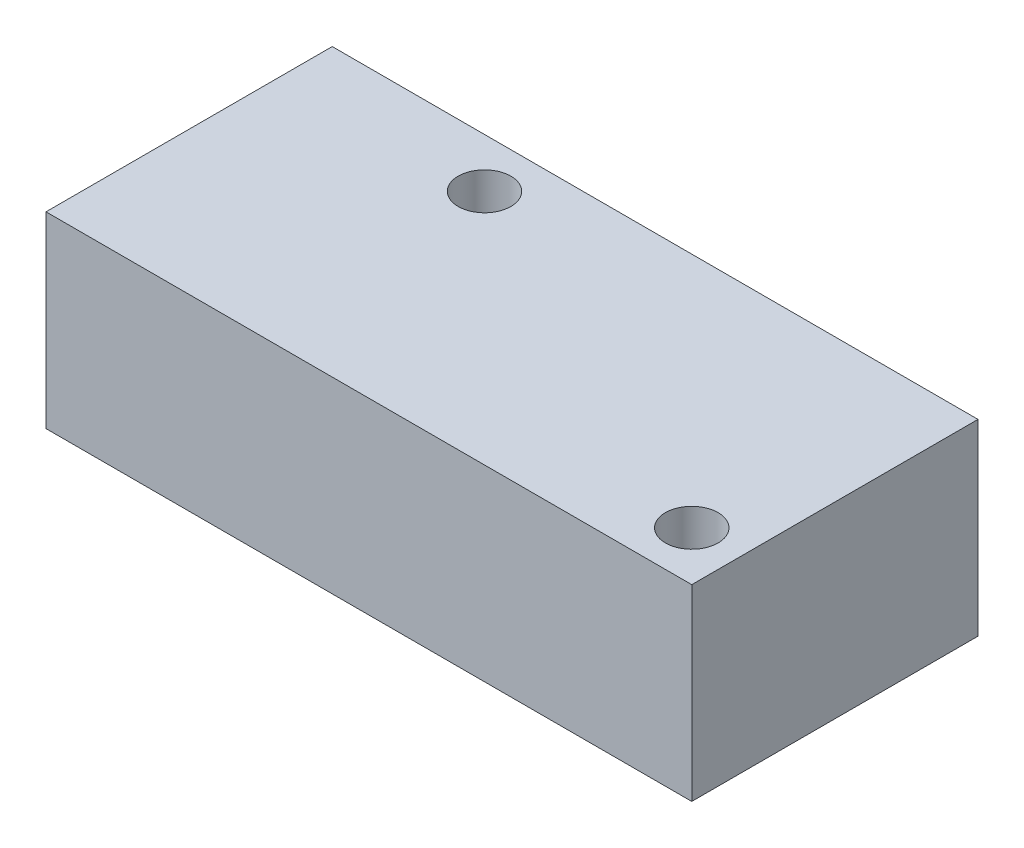
SolidWorks part; units mm, degrees
ref_plane "Front Plane" through (0, 0, 0) normal (0, 0, 1) x (1, 0, 0)
ref_plane "Top Plane" through (0, 0, 0) normal (0, 1, 0) x (1, 0, 0)
ref_plane "Right Plane" through (0, 0, 0) normal (1, 0, 0) x (0, 0, -1)
sketch "Sketch1" plane through (0, 0, 0) normal (0, 1, 0) x (1, 0, 0)
  line L0 (-0.2412, 14.605) -> (33.0328, 14.605) construction
  line L1 (-1.5112, 0) -> (34.3028, 0)
  line L2 (-1.5112, 0) -> (-1.5112, 15.875)
  line L3 (-1.5112, 15.875) -> (34.3028, 15.875)
  line L4 (34.3028, 0) -> (34.3028, 15.875)
  line L5 (33.0328, 1.27) -> (33.0328, 14.605) construction
  line L6 (-0.2412, 1.27) -> (33.0328, 1.27) construction
  line L7 (-0.2412, 1.27) -> (-0.2412, 14.605) construction
  line L8 (9.6648, 0) -> (9.6648, 15.875) construction
  circle A0 centre (9.6648, 13.1445) radius 1.4605
  circle A2 centre (31.5723, 2.7305) radius 1.4605
  dimension "D3" = 2.921
  dimension "D4" = 24.638
  dimension "D6" = 2.921
  dimension "D1" = 35.814
  dimension "D2" = 15.875
  dimension "D5" = 1.27
extrude "Boss-Extrude1" add sketch "Sketch1" along normal blind 10.414
